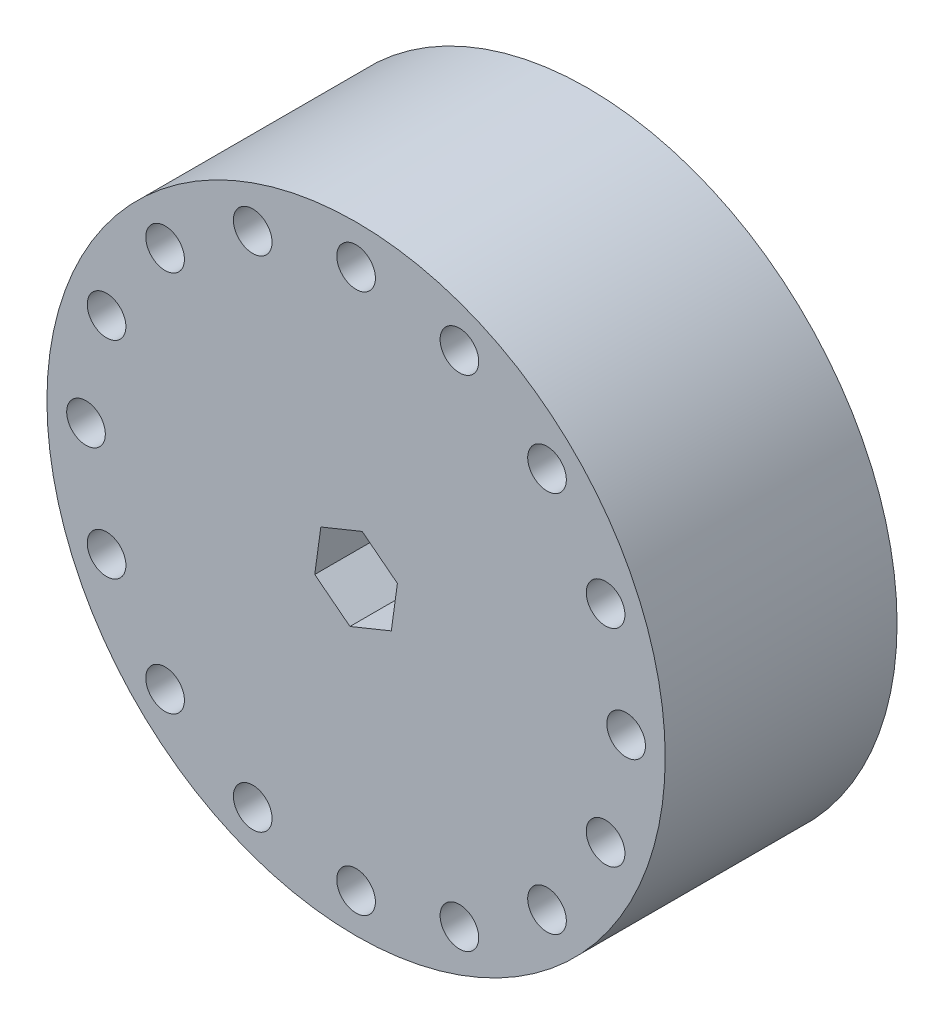
SolidWorks part; units mm, degrees
ref_plane "Front Plane" through (0, 0, 0) normal (0, 0, 1) x (1, 0, 0)
ref_plane "Top Plane" through (0, 0, 0) normal (0, 1, 0) x (1, 0, 0)
ref_plane "Right Plane" through (0, 0, 0) normal (1, 0, 0) x (0, 0, -1)
sketch "Sketch1" plane through (0, 0, 0) normal (0, 0, 1) x (1, 0, 0)
  line L1 (5.7893, -4.4996) -> (6.7915, 2.7639)
  line L2 (6.7915, 2.7639) -> (1.0021, 7.2635)
  line L3 (1.0021, 7.2635) -> (-5.7893, 4.4996)
  line L4 (-5.7893, 4.4996) -> (-6.7915, -2.7639)
  line L5 (-6.7915, -2.7639) -> (-1.0021, -7.2635)
  line L6 (-1.0021, -7.2635) -> (5.7893, -4.4996)
  circle A0 centre (0, 0) radius 50.8
  circle A1 centre (0, 0) radius 6.35 construction
  dimension "D2" = 101.6
  dimension "D1" = 12.7
extrude "Boss-Extrude1" add sketch "Sketch1" along normal blind 38.1
sketch "Sketch2" plane through (0, 0, 38.1) normal (0, 0, 1) x (1, 0, 0)
  circle A0 centre (0, 0) radius 44.3771 construction
  circle A1 centre (0, 44.3771) radius 3.175
  circle A2 centre (16.9824, 40.9991) radius 3.175
  circle A3 centre (31.3794, 31.3794) radius 3.175
  circle A4 centre (40.9991, 16.9824) radius 3.175
  circle A5 centre (44.3771, 0) radius 3.175
  circle A6 centre (40.9991, -16.9824) radius 3.175
  circle A7 centre (31.3794, -31.3794) radius 3.175
  circle A8 centre (16.9824, -40.9991) radius 3.175
  circle A9 centre (0, -44.3771) radius 3.175
  circle A10 centre (-16.9824, -40.9991) radius 3.175
  circle A11 centre (-31.3794, -31.3794) radius 3.175
  circle A12 centre (-40.9991, -16.9824) radius 3.175
  circle A13 centre (-44.3771, 0) radius 3.175
  circle A14 centre (-40.9991, 16.9824) radius 3.175
  circle A15 centre (-31.3794, 31.3794) radius 3.175
  circle A16 centre (-16.9824, 40.9991) radius 3.175
  point P37 (0, 0)
  dimension "D1" = 6.35
  dimension "D2" = 16
extrude "Cut-Extrude1" cut sketch "Sketch2" against normal through all
